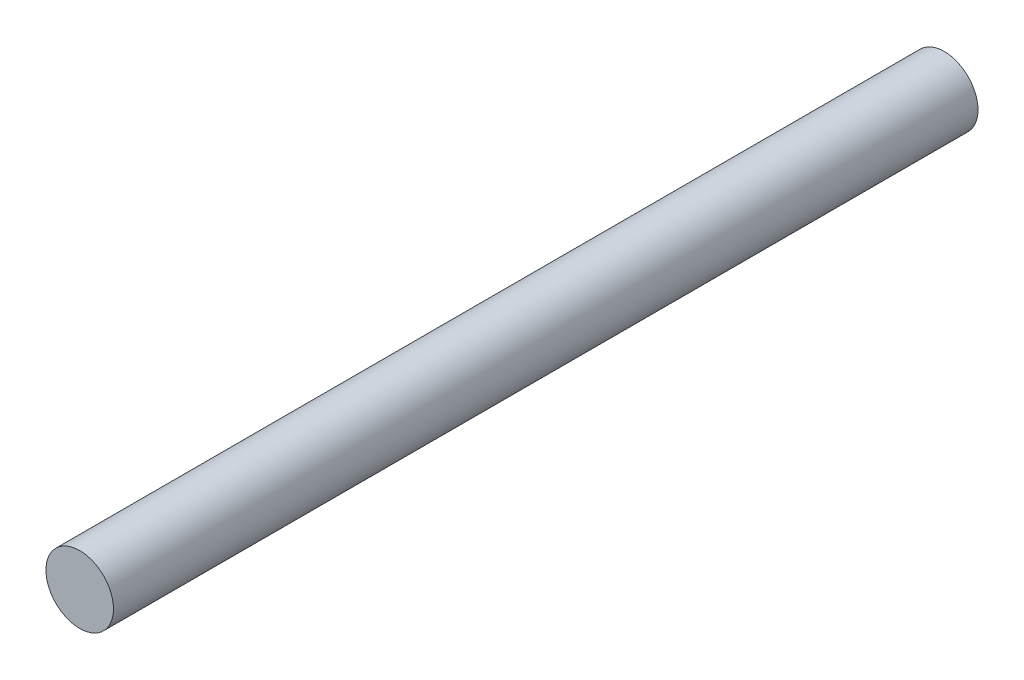
SolidWorks part; units mm, degrees
ref_plane "Front Plane" through (0, 0, 0) normal (0, 0, 1) x (1, 0, 0)
ref_plane "Top Plane" through (0, 0, 0) normal (0, 1, 0) x (1, 0, 0)
ref_plane "Right Plane" through (0, 0, 0) normal (1, 0, 0) x (0, 0, -1)
sketch "Sketch1" plane through (0, 0, 0) normal (0, 0, 1) x (1, 0, 0)
  circle A0 centre (0, 0) radius 1.5875
  dimension "D1" = 3.175
extrude "Boss-Extrude1" add sketch "Sketch1" along normal mid plane 40.64
